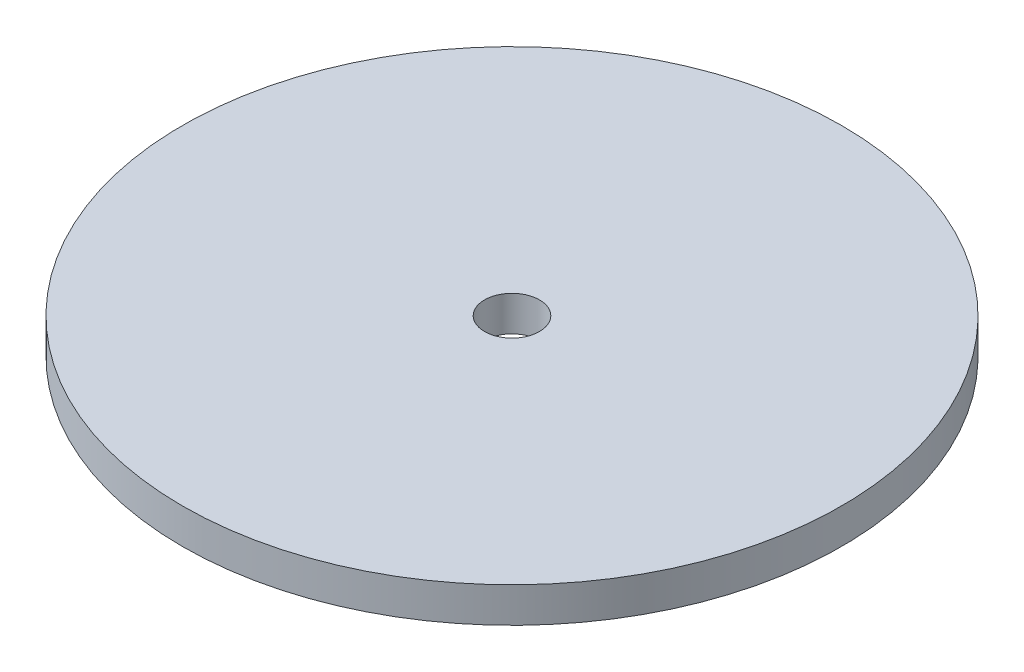
SolidWorks part; units mm, degrees
ref_plane "Front Plane" through (0, 0, 0) normal (0, 0, 1) x (1, 0, 0)
ref_plane "Top Plane" through (0, 0, 0) normal (0, 1, 0) x (1, 0, 0)
ref_plane "Right Plane" through (0, 0, 0) normal (1, 0, 0) x (0, 0, -1)
sketch "Sketch1" plane through (0, 0, 0) normal (0, 1, 0) x (1, 0, 0)
  circle A0 centre (0, 0) radius 38.1
  circle A1 centre (0, 0) radius 3.175
  dimension "D1" = 76.2
  dimension "D2" = 6.35
extrude "Boss-Extrude1" add sketch "Sketch1" along normal blind 4.064
